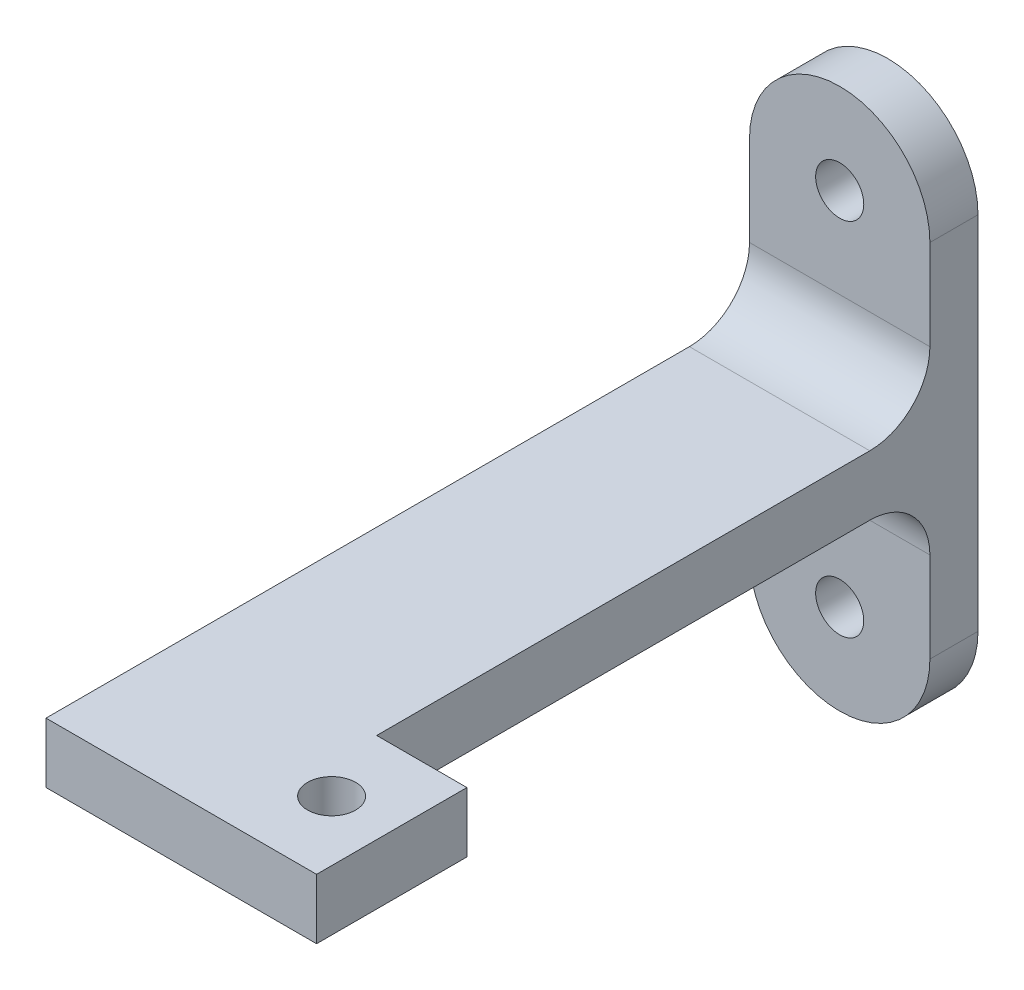
SolidWorks part; units mm, degrees
ref_plane "Front Plane" through (0, 0, 0) normal (0, 0, 1) x (1, 0, 0)
ref_plane "Top Plane" through (0, 0, 0) normal (0, 1, 0) x (1, 0, 0)
ref_plane "Right Plane" through (0, 0, 0) normal (1, 0, 0) x (0, 0, -1)
sketch "Sketch1" plane through (0, 0, 0) normal (0, 0, 1) x (1, 0, 0)
  line L0 (0, 30) -> (0, -30) construction
  line L1 (15, 30) -> (15, -30)
  line L2 (-15, 30) -> (-15, -30)
  arc A0 (15, 30) -> (-15, 30) centre (0, 30) ccw
  arc A1 (-15, -30) -> (15, -30) centre (0, -30) ccw
  circle A2 centre (0, 30) radius 4
  circle A3 centre (0, -30) radius 4
  point P3 (0, 0)
  dimension "D2" = 8
  dimension "D1" = 60
  dimension "D3" = 30
extrude "Boss-Extrude1" add sketch "Sketch1" along normal blind 8
sketch "Sketch2" plane through (0, 0, 0) normal (0, 0, 1) x (1, 0, 0)
  line L0 (15, -30) -> (15, 30) construction
  line L1 (-15, -5) -> (15, -5)
  line L2 (-15, -5) -> (-15, 5)
  line L3 (-15, 5) -> (15, 5)
  line L4 (15, -5) -> (15, 5)
  line L5 (-15, -5) -> (15, 5) construction
  line L6 (-15, 5) -> (15, -5) construction
  point P0 (0, 0)
  dimension "D1" = 10
extrude "Boss-Extrude2" add sketch "Sketch2" along normal blind 100
fillet "Fillet1" radius 10 2 edges at (0, -5, 8) (0, 5, 8)
sketch "Sketch5" plane through (0, 5, 0) normal (0, 1, 0) x (1, 0, 0)
  line L0 (0, 0) -> (0, -125) construction
  line L1 (-15, -100) -> (30, -100)
  line L2 (-15, -100) -> (-15, -125)
  line L3 (-15, -125) -> (30, -125)
  line L4 (30, -100) -> (30, -125)
  line L5 (-15, -112.5) -> (0, -112.5) construction
  line L6 (0, -112.5) -> (20, -112.5) construction
  circle A0 centre (20, -112.5) radius 4
  point P12 (30, -112.5)
  dimension "D2" = 8
  dimension "D1" = 25
  dimension "D3" = 20
  dimension "D4" = 10
extrude "Boss-Extrude4" add sketch "Sketch5" against normal up to surface (10 mm away) up to face at (0, -5, 59)
